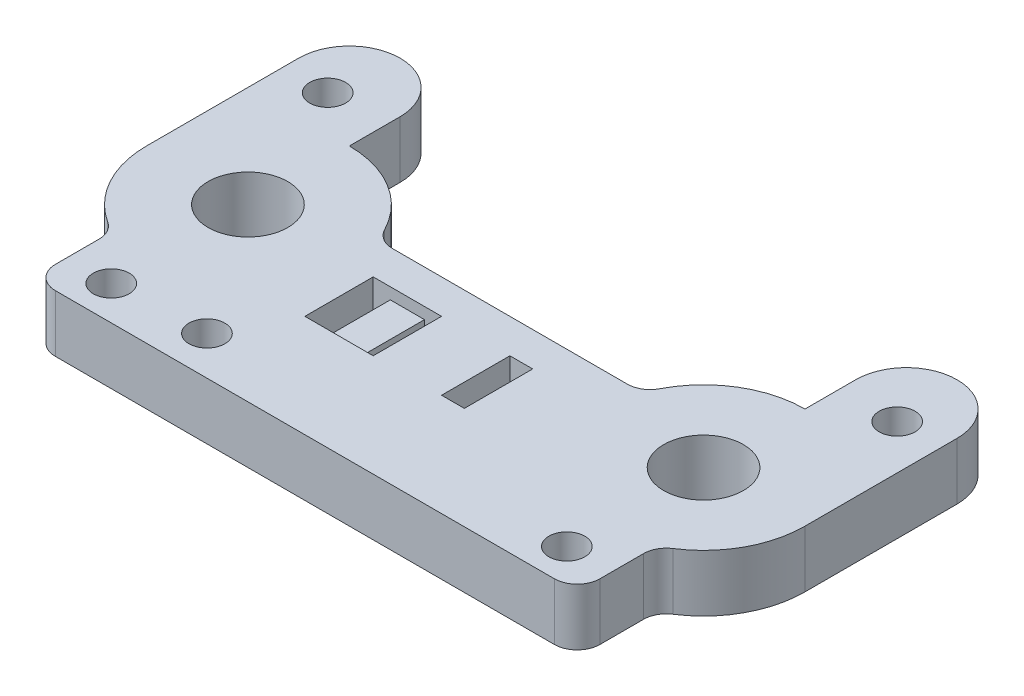
SolidWorks part; units mm, degrees
ref_plane "Front Plane" through (0, 0, 0) normal (0, 0, 1) x (1, 0, 0)
ref_plane "Top Plane" through (0, 0, 0) normal (0, 1, 0) x (1, 0, 0)
ref_plane "Right Plane" through (0, 0, 0) normal (1, 0, 0) x (0, 0, -1)
sketch "Sketch1" plane through (0, 0, 0) normal (0, 1, 0) x (1, 0, 0)
  line L0 (-25.4, 0) -> (25.4, 0) construction
  line L1 (-25.4, 16.965) -> (-25.4, 11.31)
  line L2 (-27.82, -19.05) -> (27.82, -19.05)
  line L3 (-13.0915, 3.81) -> (13.0915, 3.81)
  line L4 (-36.71, 11.31) -> (-36.71, 0)
  line L5 (36.71, 0) -> (36.71, 11.31)
  line L6 (-30.36, -16.51) -> (-30.36, -11.6436)
  line L7 (25.4, 16.965) -> (25.4, 11.31)
  line L9 (30.36, -16.51) -> (30.36, -11.6436)
  line L10 (-36.71, 16.965) -> (-36.71, 11.31)
  line L12 (36.71, 16.965) -> (36.71, 0)
  arc A0 (-25.4, 16.965) -> (-36.71, 16.965) centre (-31.055, 16.965) ccw
  arc A1 (36.71, 16.965) -> (25.4, 16.965) centre (31.055, 16.965) ccw
  arc A2 (25.4, 11.31) -> (16.5089, 6.9903) centre (25.4, 0) ccw
  arc A3 (-25.4, 11.31) -> (-16.5089, 6.9903) centre (-25.4, 0) cw
  arc A4 (25.4, 11.31) -> (15.3488, 5.1855) centre (25.4, 0) ccw
  arc A5 (-15.3488, 5.1855) -> (-25.4, 11.31) centre (-25.4, 0) ccw
  arc A6 (-13.0915, 3.81) -> (-15.3488, 5.1855) centre (-13.0915, 6.35) cw
  arc A7 (15.3488, 5.1855) -> (13.0915, 3.81) centre (13.0915, 6.35) cw
  arc A8 (25.4, 11.31) -> (14.09, 0) centre (25.4, 0) ccw
  arc A9 (-30.36, -11.6436) -> (-31.5245, -9.5082) centre (-32.9, -11.6436) ccw
  arc A10 (-36.71, 0) -> (-31.5245, -9.5082) centre (-25.4, 0) ccw
  arc A11 (31.5245, -9.5082) -> (30.36, -11.6436) centre (32.9, -11.6436) ccw
  arc A12 (14.09, 0) -> (25.4, 11.31) centre (25.4, 0) cw
  arc A13 (36.71, 0) -> (31.5245, -9.5082) centre (25.4, 0) cw
  arc A15 (27.82, -19.05) -> (30.36, -16.51) centre (27.82, -16.51) ccw
  arc A16 (-27.82, -19.05) -> (-30.36, -16.51) centre (-27.82, -16.51) cw
  point P2 (0, 0)
  point P3 (0, -11.31)
  point P10 (-6.35, -11.31)
  point P21 (6.35, -11.31)
  point P31 (25.4, -11.31)
  dimension "D2" = 2.54
  dimension "D6" = 11.31
  dimension "D7" = 2.54
  dimension "D8" = 36.71
  dimension "D5" = 11.31
  dimension "D9" = 2.54
  dimension "D10" = 19.05
  dimension "D11" = 2.54
  dimension "D1" = 50.8
  dimension "D4" = 3.81
extrude "Boss-Extrude1" add sketch "Sketch1" along normal blind 6.35
sketch "Sketch3" plane through (0, 6.35, 0) normal (0, 1, 0) x (1, 0, 0)
  line L0 (0, 0) -> (0, 8.8907) construction
  circle A0 centre (-25.4, 0) radius 4.445
  circle A1 centre (25.4, 0) radius 4.445
  point P8 (-56.9686, 21.9501)
  dimension "D1" = 8.89
extrude "Cut-Extrude2" cut sketch "Sketch3" against normal blind 6.35
sketch "Sketch8" plane through (0, 6.35, 0) normal (0, 1, 0) x (1, 0, 0)
  circle A0 centre (-31.75, 15.24) radius 2
  circle A1 centre (25.4, -15.24) radius 2
  circle A2 centre (-25.4, -15.24) radius 2
  circle A3 centre (31.75, 15.24) radius 2
  point P13 (23.6789, -11.6813)
  point P14 (26.5787, -11.0843)
  point P15 (20.2534, -11.6206)
  point P16 (0, 0)
  point P17 (33.5325, 13.0897)
  dimension "D1" = 15.24
  dimension "D3" = 4
  dimension "D4" = 4
  dimension "D7" = 4
  dimension "D8" = 4
  dimension "D2" = 15.24
  dimension "D5" = 25.4
  dimension "D6" = 25.4
  dimension "D9" = 15.24
  dimension "D10" = 31.75
  dimension "D11" = 31.75
  dimension "D12" = 15.24
sketch "Sketch11" plane through (0, 6.35, 0) normal (0, 1, 0) x (1, 0, 0)
  line L0 (-13.1155, 0) -> (12.0576, 0) construction
  line L1 (-13.1155, -7.62) -> (12.0576, -7.62) construction
  line L3 (3.81, 0) -> (6.35, 0)
  line L4 (3.81, 0) -> (3.81, -7.62)
  line L5 (3.81, -7.62) -> (6.35, -7.62)
  line L6 (6.35, 0) -> (6.35, -7.62)
  line L7 (-3.81, 0) -> (-5.715, 0)
  line L8 (-3.81, 0) -> (-3.81, -7.62)
  line L9 (-3.81, -7.62) -> (-5.715, -7.62)
  line L10 (-5.715, 0) -> (-5.715, -7.62)
  line L11 (-9.525, 0) -> (-11.43, 0)
  line L12 (-9.525, 0) -> (-9.525, -7.62)
  line L13 (-9.525, -7.62) -> (-11.43, -7.62)
  line L14 (-11.43, 0) -> (-11.43, -7.62)
  dimension "D1" = 7.62
  dimension "D2" = 1.905
  dimension "D3" = 1.905
  dimension "D4" = 2.54
  dimension "D5" = 3.81
  dimension "D6" = 3.81
  dimension "D7" = 3.81
extrude "Cut-Extrude6" cut sketch "Sketch11" against normal blind 6.35
sketch "Sketch14" plane through (0, 6.35, 0) normal (0, 1, 0) x (1, 0, 0)
  line L0 (-5.715, 0) -> (-5.715, -7.62) construction
  line L1 (-9.525, 0) -> (-5.715, 0)
  line L2 (-9.525, 0) -> (-9.525, -7.62)
  line L3 (-9.525, -7.62) -> (-5.715, -7.62)
  line L4 (-5.715, 0) -> (-5.715, -7.62)
  line L5 (-5.715, -7.62) -> (-3.81, -7.62) construction
extrude "Cut-Extrude8" cut sketch "Sketch14" against normal blind 1.27
extrude "Cut-Extrude10" cut sketch "Sketch8" against normal blind 6.35
sketch "Sketch15" plane through (0, 6.35, 0) normal (0, 1, 0) x (1, 0, 0)
  circle A0 centre (-15.24, -14.732) radius 2
  dimension "D1" = 15.24
  dimension "D3" = 4
  dimension "D2" = 14.732
extrude "Cut-Extrude11" cut sketch "Sketch15" against normal blind 6.35
